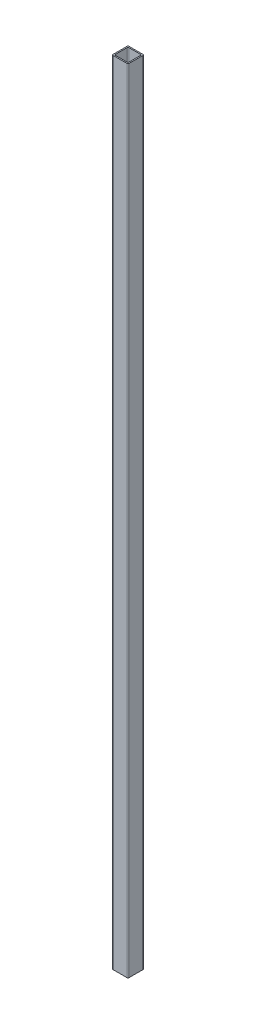
SolidWorks part; units mm, degrees
material "Hexcel AS4C (3000 Filaments)"
ref_plane "Front Plane" through (0, 0, 0) normal (0, 0, 1) x (1, 0, 0)
ref_plane "Top Plane" through (0, 0, 0) normal (0, 1, 0) x (1, 0, 0)
ref_plane "Right Plane" through (0, 0, 0) normal (1, 0, 0) x (0, 0, -1)
sketch "Sketch1" plane through (0, 0, 0) normal (0, 1, 0) x (1, 0, 0)
  line L1 (-9, -10) -> (9, -10)
  line L2 (-10, -9) -> (-10, 9)
  line L3 (-9, 10) -> (9, 10)
  line L4 (10, -9) -> (10, 9)
  line L5 (-10, -10) -> (10, 10) construction
  line L6 (-10, 10) -> (10, -10) construction
  line L7 (-7.5, -8.5) -> (7.5, -8.5)
  line L8 (-8.5, -7.5) -> (-8.5, 7.5)
  line L9 (-7.5, 8.5) -> (7.5, 8.5)
  line L10 (8.5, -7.5) -> (8.5, 7.5)
  line L11 (-8.5, -8.5) -> (8.5, 8.5) construction
  line L12 (-8.5, 8.5) -> (8.5, -8.5) construction
  arc A0 (-9, -10) -> (-10, -9) centre (-9, -9) cw
  arc A1 (9, 10) -> (10, 9) centre (9, 9) cw
  arc A2 (9, -10) -> (10, -9) centre (9, -9) ccw
  arc A3 (-10, 9) -> (-9, 10) centre (-9, 9) cw
  arc A4 (-7.5, -8.5) -> (-8.5, -7.5) centre (-7.5, -7.5) cw
  arc A5 (7.5, -8.5) -> (8.5, -7.5) centre (7.5, -7.5) ccw
  arc A6 (7.5, 8.5) -> (8.5, 7.5) centre (7.5, 7.5) cw
  arc A7 (-8.5, 7.5) -> (-7.5, 8.5) centre (-7.5, 7.5) cw
  point P0 (0, 0)
  point P18 (0, 0)
  dimension "D3" = 1
  dimension "D6" = 1
  dimension "D7" = 1
  dimension "D8" = 1
  dimension "D9" = 1
  dimension "D1" = 20
  dimension "D2" = 20
  dimension "D4" = 17
  dimension "D5" = 17
extrude "Boss-Extrude1" add sketch "Sketch1" along normal blind 1000
